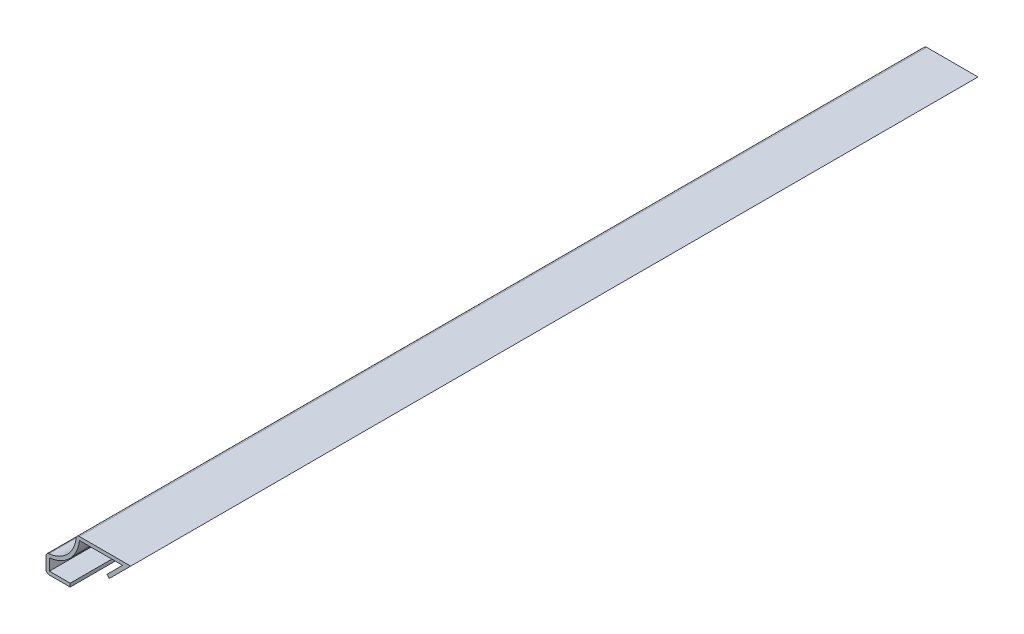
SolidWorks part; units mm, degrees
ref_plane "Front Plane" through (0, 0, 0) normal (0, 0, 1) x (1, 0, 0)
ref_plane "Top Plane" through (0, 0, 0) normal (0, 1, 0) x (1, 0, 0)
ref_plane "Right Plane" through (0, 0, 0) normal (1, 0, 0) x (0, 0, -1)
sketch "Sketch1" plane through (0, 0, 0) normal (0, 0, 1) x (1, 0, 0)
  line L0 (0, 0) -> (-6.35, 0)
  line L1 (-6.35, 0) -> (-6.35, 4.7625)
  line L2 (1.5875, 12.7) -> (15.875, 12.7)
  line L3 (15.875, 12.7) -> (10.2623, 7.0873)
  arc A0 (-6.35, 4.7625) -> (1.5875, 12.7) centre (-6.35, 12.7) ccw
extrude "Extrude-Thin1" add sketch "Sketch1" against normal blind 222.25 thin
fillet "Fillet1" radius 0.889 3 edges at (-6.35, 4.7625, -111.125) (-6.35, 0, -111.125) (1.5875, 12.7, -111.125)
equation "\"D1@Extrude-Thin1\"=\"D4@Sketch1\"*10"
